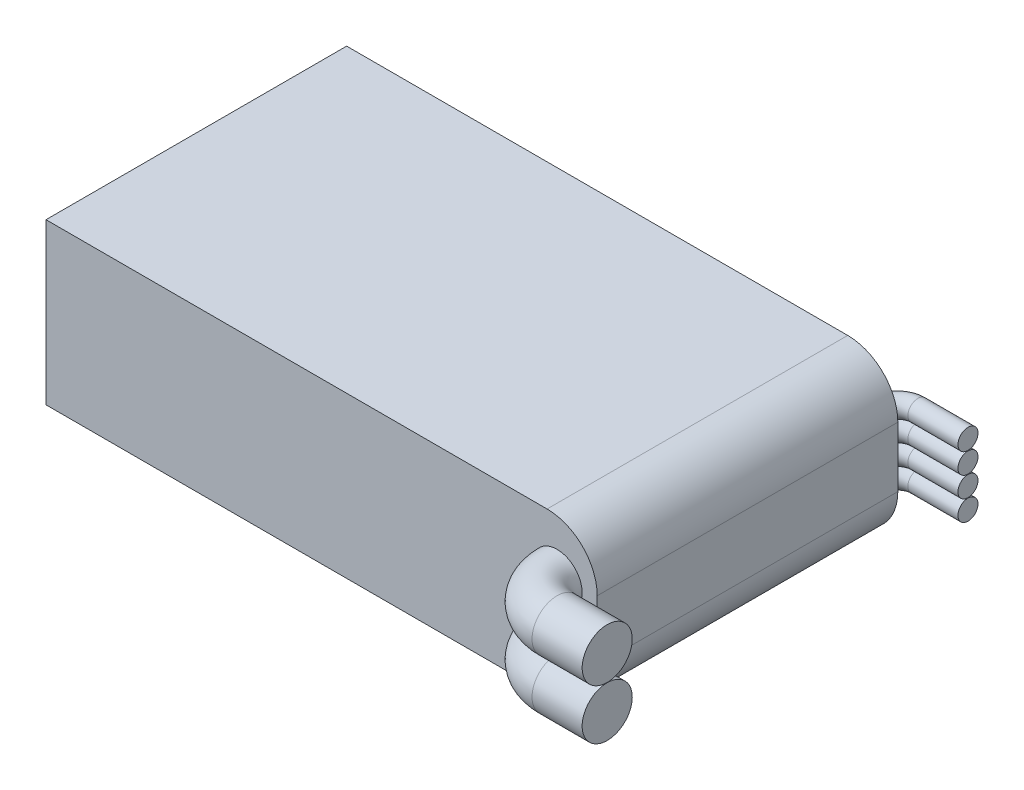
SolidWorks part; units mm, degrees
ref_plane "Front Plane" through (0, 0, 0) normal (0, 0, 1) x (1, 0, 0)
ref_plane "Top Plane" through (0, 0, 0) normal (0, 1, 0) x (1, 0, 0)
ref_plane "Right Plane" through (0, 0, 0) normal (1, 0, 0) x (0, 0, -1)
sketch "Sketch1" plane through (0, 0, 0) normal (0, 1, 0) x (1, 0, 0)
  line L1 (-27.5, -15) -> (27.5, -15)
  line L2 (-27.5, -15) -> (-27.5, 15)
  line L3 (-27.5, 15) -> (27.5, 15)
  line L4 (27.5, -15) -> (27.5, 15)
  line L5 (-27.5, -15) -> (27.5, 15) construction
  line L6 (-27.5, 15) -> (27.5, -15) construction
  point P0 (0, 0)
  dimension "D1" = 30
  dimension "D2" = 55
extrude "Boss-Extrude1" add sketch "Sketch1" along normal blind 16
fillet "Fillet1" radius 5 2 edges at (27.5, 0, 0) (27.5, 16, 0)
sketch "Sketch2" plane through (0, 0, 15) normal (0, 0, 1) x (1, 0, 0)
  line L0 (27.5, 11) -> (27.5, 5) construction
  line L2 (27.5, 8) -> (-27.5, 8) construction
  line L3 (-27.5, 16) -> (-27.5, 0) construction
  circle A0 centre (23.5, 10.51) radius 2.5
  circle A1 centre (23.5, 5.49) radius 2.5
  point P10 (23.5, 10.5467)
  dimension "D1" = 5
  dimension "D2" = 5
  dimension "D3" = 4
  dimension "D4" = 2.51
  dimension "D5" = 2.51
sketch "Sketch7" plane through (0, 0, 0) normal (0, -1, 0) x (-1, 0, 0)
  line L1 (-27.5, -19) -> (-32.5, -19)
  line L3 (27.5, -15) -> (-22.5, -15) construction
  arc A0 (-27.5, -19) -> (-23.5, -15) centre (-27.5, -15) ccw
  dimension "D1" = 4
  dimension "D2" = 5
sweep "Sweep5" add profiles "Sketch2" path "Sketch7"
sketch "Sketch9" plane through (0, 0, -15) normal (0, 0, -1) x (-1, 0, 0)
  line L0 (-27.5, 8) -> (27.5, 8) construction
  line L1 (-27.5, 11) -> (-27.5, 5) construction
  line L2 (27.5, 16) -> (27.5, 0) construction
  circle A0 centre (-25.5, 9.02) radius 1
  circle A1 centre (-25.5, 6.98) radius 1
  circle A2 centre (-25.5, 11.06) radius 1
  circle A3 centre (-25.5, 4.94) radius 1
  dimension "D1" = 2
  dimension "D4" = 2
  dimension "D6" = 2
  dimension "D8" = 2
  dimension "D2" = 2
  dimension "D3" = 1.02
  dimension "D5" = 1.02
  dimension "D7" = 2.04
  dimension "D9" = 2.04
sketch "Sketch10" plane through (0, 0, 0) normal (0, 1, 0) x (1, 0, 0)
  line L0 (26.5, 15) -> (24.5, 15) construction
  line L2 (27.5, 17) -> (32.5, 17)
  line L3 (27.5, 15) -> (-27.5, 15) construction
  line L4 (32.5, -21.5) -> (32.5, -16.5) construction
  arc A0 (25.5, 15) -> (27.5, 17) centre (27.5, 15) cw
  dimension "D1" = 2
sweep "Sweep6" add profiles "Sketch9" path "Sketch10"
